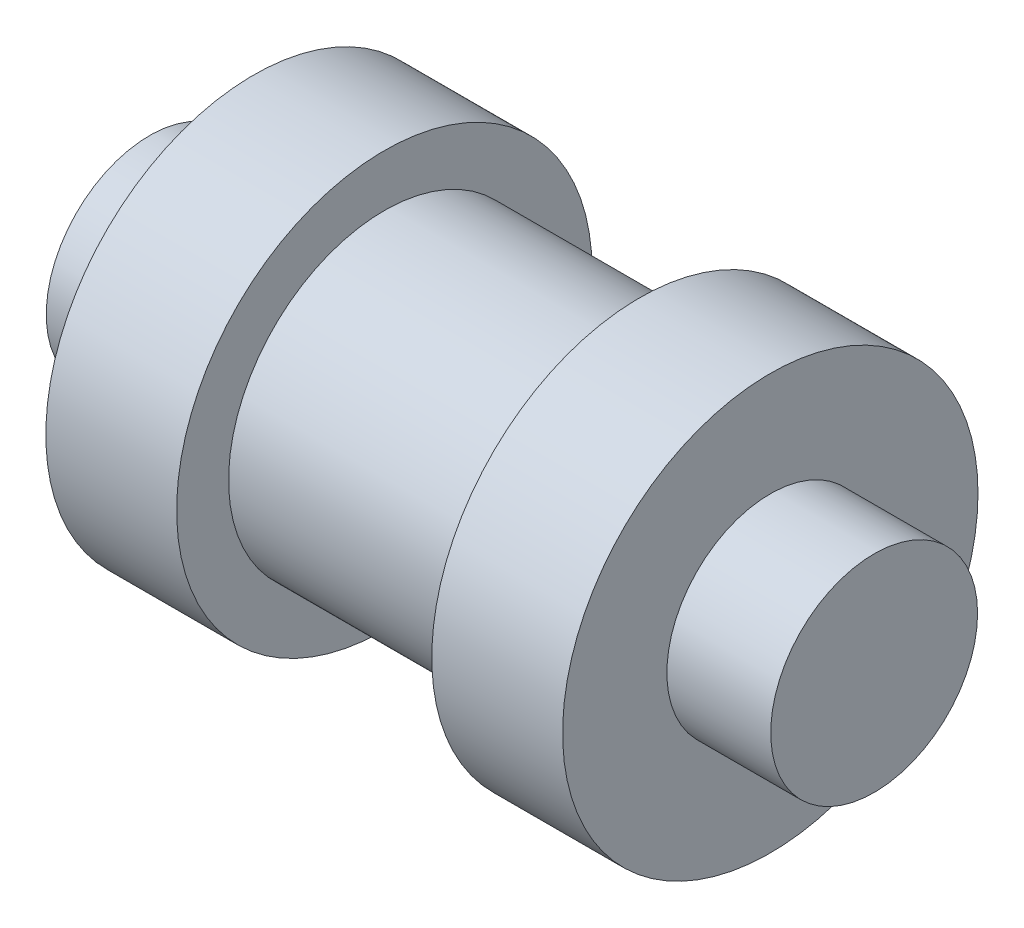
SolidWorks part; units mm, degrees
ref_plane "Front Plane" through (0, 0, 0) normal (0, 0, 1) x (1, 0, 0)
ref_plane "Top Plane" through (0, 0, 0) normal (0, 1, 0) x (1, 0, 0)
ref_plane "Right Plane" through (0, 0, 0) normal (1, 0, 0) x (0, 0, -1)
sketch "Sketch1" plane through (0, 0, 0) normal (0, 0, 1) x (1, 0, 0)
  line L0 (5.5375, 0) -> (-5.5375, 0)
  line L1 (-5.5375, 0) -> (-5.5375, 1.5811)
  line L2 (-5.5375, 1.5811) -> (-3.95, 1.5811)
  line L3 (-3.95, 1.5811) -> (-3.95, 3.175)
  line L4 (-3.95, 3.175) -> (-1.95, 3.175)
  line L5 (-1.95, 3.175) -> (-1.95, 2.3812)
  line L6 (-1.95, 2.3812) -> (1.95, 2.3812)
  line L7 (11.7977, 0) -> (-12.7325, 0) construction
  line L8 (0, 4.6891) -> (0, -2.1369) construction
  line L9 (1.95, 3.175) -> (1.95, 2.3812)
  line L10 (3.95, 3.175) -> (1.95, 3.175)
  line L11 (3.95, 1.5811) -> (3.95, 3.175)
  line L12 (5.5375, 1.5811) -> (3.95, 1.5811)
  line L13 (5.5375, 0) -> (5.5375, 1.5811)
  point P14 (0, 2.3812)
  point P19 (0, 0)
  dimension "D1" = 3.95
  dimension "D2" = 2
  dimension "D3" = 1.5811
  dimension "D4" = 3.175
  dimension "D5" = 2.3813
  dimension "D6" = 1.5875
revolve "Revolve1" add sketch "Sketch1" angle 360 about L7
sketch "Sketch2" plane through (-5.5375, 0, 0) normal (-1, 0, 0) x (0, 0, 1)
  point P0 (0, 0)
